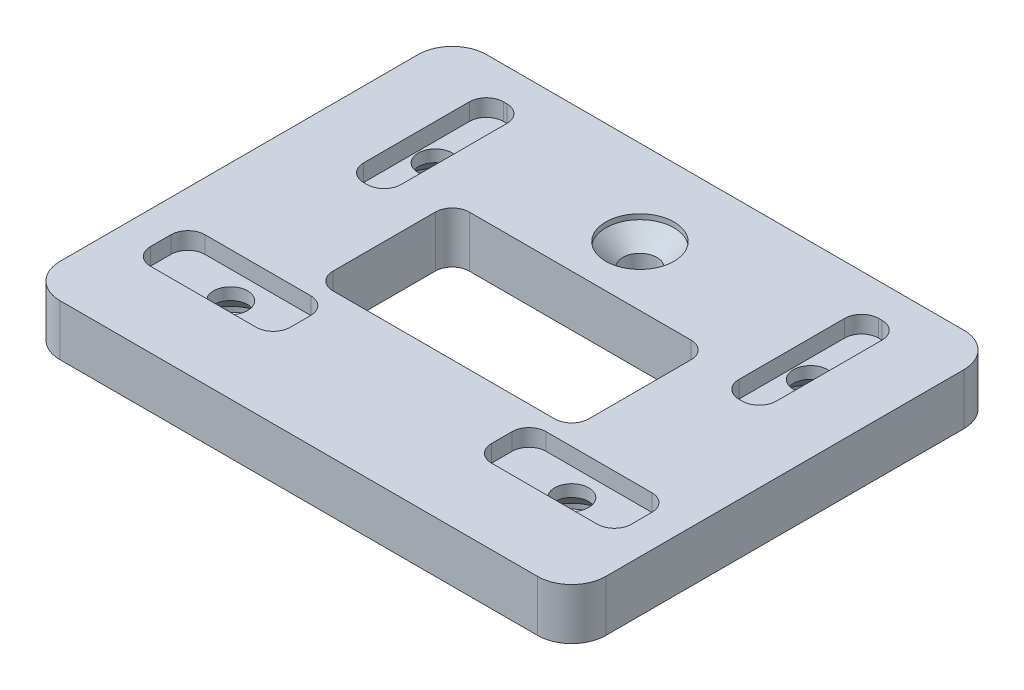
SolidWorks part; units mm, degrees
ref_plane "Front Plane" through (0, 0, 0) normal (0, 0, 1) x (1, 0, 0)
ref_plane "Top Plane" through (0, 0, 0) normal (0, 1, 0) x (1, 0, 0)
ref_plane "Right Plane" through (0, 0, 0) normal (1, 0, 0) x (0, 0, -1)
sketch "Sketch1" plane through (0, 0, 0) normal (0, 1, 0) x (1, 0, 0)
  line L1 (16, 12.5) -> (-16, 12.5)
  line L2 (16, 12.5) -> (16, -12.5)
  line L3 (16, -12.5) -> (-16, -12.5)
  line L4 (-16, 12.5) -> (-16, -12.5)
  line L5 (16, 12.5) -> (-16, -12.5) construction
  line L6 (16, -12.5) -> (-16, 12.5) construction
  point P0 (0, 0)
  dimension "D1" = 32
  dimension "D2" = 25
extrude "Boss-Extrude1" add sketch "Sketch1" along normal blind 3
sketch "Sketch2" plane through (0, 3, 0) normal (0, 1, 0) x (1, 0, 0)
  line L0 (-16, -6.5) -> (16, -6.5) construction
  line L1 (-16, 12.5) -> (-16, -12.5) construction
  line L2 (16, -12.5) -> (16, 12.5) construction
  line L3 (0, 12.5) -> (0, -12.5) construction
  line L4 (16, 12.5) -> (-16, 12.5) construction
  line L5 (-16, -12.5) -> (16, -12.5) construction
  line L6 (14.1, -5.9) -> (14.1, -7.1)
  line L7 (-13.1, -4.9) -> (-6.9, -4.9)
  line L8 (-14.1, -5.9) -> (-14.1, -7.1)
  line L9 (-13.1, -8.1) -> (-6.9, -8.1)
  line L10 (-5.9, -5.9) -> (-5.9, -7.1)
  line L11 (-14.1, -4.9) -> (-5.9, -8.1) construction
  line L12 (-14.1, -8.1) -> (-5.9, -4.9) construction
  line L13 (13.1, -4.9) -> (6.9, -4.9)
  line L14 (5.9, -5.9) -> (5.9, -7.1)
  line L15 (13.1, -8.1) -> (6.9, -8.1)
  line L16 (11.1, 10.6) -> (10.9, 10.6)
  line L17 (-11.1, 10.6) -> (-10.9, 10.6)
  line L18 (-12.1, 9.6) -> (-12.1, 3.4)
  line L19 (-11.1, 2.4) -> (-10.9, 2.4)
  line L20 (-9.9, 9.6) -> (-9.9, 3.4)
  line L21 (-12.1, 10.6) -> (-9.9, 2.4) construction
  line L22 (-12.1, 2.4) -> (-9.9, 10.6) construction
  line L23 (12.1, 9.6) -> (12.1, 3.4)
  line L24 (11.1, 2.4) -> (10.9, 2.4)
  line L25 (9.9, 9.6) -> (9.9, 3.4)
  arc A0 (-14.1, -7.1) -> (-13.1, -8.1) centre (-13.1, -7.1) ccw
  arc A1 (-6.9, -8.1) -> (-5.9, -7.1) centre (-6.9, -7.1) ccw
  arc A2 (-6.9, -4.9) -> (-5.9, -5.9) centre (-6.9, -5.9) cw
  arc A3 (-13.1, -4.9) -> (-14.1, -5.9) centre (-13.1, -5.9) ccw
  arc A4 (14.1, -7.1) -> (13.1, -8.1) centre (13.1, -7.1) cw
  arc A5 (13.1, -4.9) -> (14.1, -5.9) centre (13.1, -5.9) cw
  arc A6 (6.9, -4.9) -> (5.9, -5.9) centre (6.9, -5.9) ccw
  arc A7 (6.9, -8.1) -> (5.9, -7.1) centre (6.9, -7.1) cw
  arc A8 (-10.9, 2.4) -> (-9.9, 3.4) centre (-10.9, 3.4) ccw
  arc A9 (-12.1, 3.4) -> (-11.1, 2.4) centre (-11.1, 3.4) ccw
  arc A10 (-10.9, 10.6) -> (-9.9, 9.6) centre (-10.9, 9.6) cw
  arc A11 (-11.1, 10.6) -> (-12.1, 9.6) centre (-11.1, 9.6) ccw
  arc A12 (11.1, 10.6) -> (12.1, 9.6) centre (11.1, 9.6) cw
  arc A13 (12.1, 3.4) -> (11.1, 2.4) centre (11.1, 3.4) cw
  arc A14 (10.9, 2.4) -> (9.9, 3.4) centre (10.9, 3.4) cw
  arc A15 (10.9, 10.6) -> (9.9, 9.6) centre (10.9, 9.6) ccw
  point P12 (-10, -6.5)
  point P41 (-11, 6.5)
  dimension "D5" = 1
  dimension "D10" = 1
  dimension "D1" = 6
  dimension "D2" = 20
  dimension "D3" = 8.2
  dimension "D4" = 3.2
  dimension "D6" = 8.2
  dimension "D7" = 2.2
  dimension "D8" = 22
  dimension "D9" = 6
extrude "Cut-Extrude1" cut sketch "Sketch2" against normal blind 1
sketch "Sketch3" plane through (0, 2, 0) normal (0, 1, 0) x (1, 0, 0)
  line L0 (-10, -4.9) -> (-10, -8.1) construction
  line L1 (-6.9, -4.9) -> (-13.1, -4.9) construction
  line L2 (-13.1, -8.1) -> (-6.9, -8.1) construction
  line L3 (0, 12.5) -> (0, -12.5) construction
  line L4 (16, 12.5) -> (-16, 12.5) construction
  line L5 (-16, -12.5) -> (16, -12.5) construction
  line L6 (-12.1, 6.5) -> (-9.9, 6.5) construction
  line L7 (-12.1, 9.6) -> (-12.1, 3.4) construction
  line L8 (-9.9, 3.4) -> (-9.9, 9.6) construction
  circle A0 centre (-10, -6.5) radius 1
  circle A1 centre (10, -6.5) radius 1
  circle A2 centre (-11, 6.5) radius 1
  circle A3 centre (11, 6.5) radius 1
  dimension "D1" = 2
extrude "Cut-Extrude2" cut sketch "Sketch3" against normal up to next
sketch "Sketch4" plane through (0, 3, 0) normal (0, 1, 0) x (1, 0, 0)
  line L0 (0, 12.5) -> (0, -12.5) construction
  line L1 (16, 12.5) -> (-16, 12.5) construction
  line L2 (-16, -12.5) -> (16, -12.5) construction
  line L3 (-16, 0) -> (16, 0) construction
  line L6 (-16, 12.5) -> (-16, -12.5) construction
  line L7 (16, -12.5) -> (16, 12.5) construction
  circle A5 centre (0, 7.5) radius 1
  point P8 (0, 0)
  dimension "D1" = 2
  dimension "D2" = 5
extrude "Cut-Extrude3" cut sketch "Sketch4" against normal up to next
hole_wizard "CSK for M2 Flat Head Machine Screw4" positions "Sketch11" profile "Sketch12" countersink size "M2" standard "ANSI Metric" end condition up to next
sketch "Sketch11" plane through (0, 3, 0) normal (0, 1, 0) x (1, 0, 0)
  point P0 (0, 7.5)
  point P5 (0, 7.5)
sketch "Sketch12" plane through (0, 3, -7.5) normal (1, 0, 0) x (0, 0, 1)
  line L0 (0, 0) -> (0, 3)
  line L1 (0, 3) -> (1, 3)
  line L2 (1, 3) -> (1, 1.3)
  line L3 (1, 1.3) -> (2, 0.3)
  line L4 (2, 0.3) -> (2, 0)
  line L6 (2, 0) -> (0, 0)
  line L7 (-1, 1.3) -> (-2, 0.3) construction
  line L11 (0, -6.35) -> (0, 107.95) construction
  dimension "Thru Hole Dia." = 2
  dimension "Thru Hole Depth" = 3
  dimension "C'Sink Dia." = 4
  dimension "C'Sink Angle" = 90
  dimension "Head Clearance" = 0.3
fillet "Fillet1" radius 2 4 edges at (-16, 1.5, -12.5) (16, 1.5, -12.5) (16, 1.5, 12.5) (-16, 1.5, 12.5)
sketch "Sketch13" plane through (0, 3, 0) normal (0, 1, 0) x (1, 0, 0)
  line L1 (6.5, 4) -> (-6.5, 4)
  line L2 (7.5, 3) -> (7.5, -3)
  line L3 (6.5, -4) -> (-6.5, -4)
  line L4 (-7.5, 3) -> (-7.5, -3)
  line L5 (7.5, 4) -> (-7.5, -4) construction
  line L6 (7.5, -4) -> (-7.5, 4) construction
  arc A0 (6.5, 4) -> (7.5, 3) centre (6.5, 3) cw
  arc A1 (7.5, -3) -> (6.5, -4) centre (6.5, -3) cw
  arc A2 (-6.5, -4) -> (-7.5, -3) centre (-6.5, -3) cw
  arc A3 (-6.5, 4) -> (-7.5, 3) centre (-6.5, 3) ccw
  point P0 (0, 0)
  dimension "D3" = 1
  dimension "D1" = 15
  dimension "D2" = 8
extrude "Cut-Extrude4" cut sketch "Sketch13" against normal up to next
hole_wizard "CSK for M2 Flat Head Machine Screw5" positions "Sketch14" profile "Sketch15" countersink size "M2" standard "ANSI Metric" end condition up to next
sketch "Sketch14" plane through (0, 0, 0) normal (0, -1, 0) x (-1, 0, 0)
  point P0 (-11, 6.5)
  point P3 (11, 6.5)
  point P6 (-10, -6.5)
  point P9 (10, -6.5)
sketch "Sketch15" plane through (11, 0, -6.5) normal (1, 0, 0) x (0, 0, -1)
  line L0 (0, 0) -> (0, 3)
  line L1 (0, 3) -> (1, 3)
  line L2 (1, 3) -> (1, 1.3)
  line L3 (1, 1.3) -> (2, 0.3)
  line L4 (2, 0.3) -> (2, 0)
  line L6 (2, 0) -> (0, 0)
  line L7 (-1, 1.3) -> (-2, 0.3) construction
  line L11 (0, -6.35) -> (0, 107.95) construction
  dimension "Thru Hole Dia." = 2
  dimension "Thru Hole Depth" = 3
  dimension "C'Sink Dia." = 4
  dimension "C'Sink Angle" = 90
  dimension "Head Clearance" = 0.3
